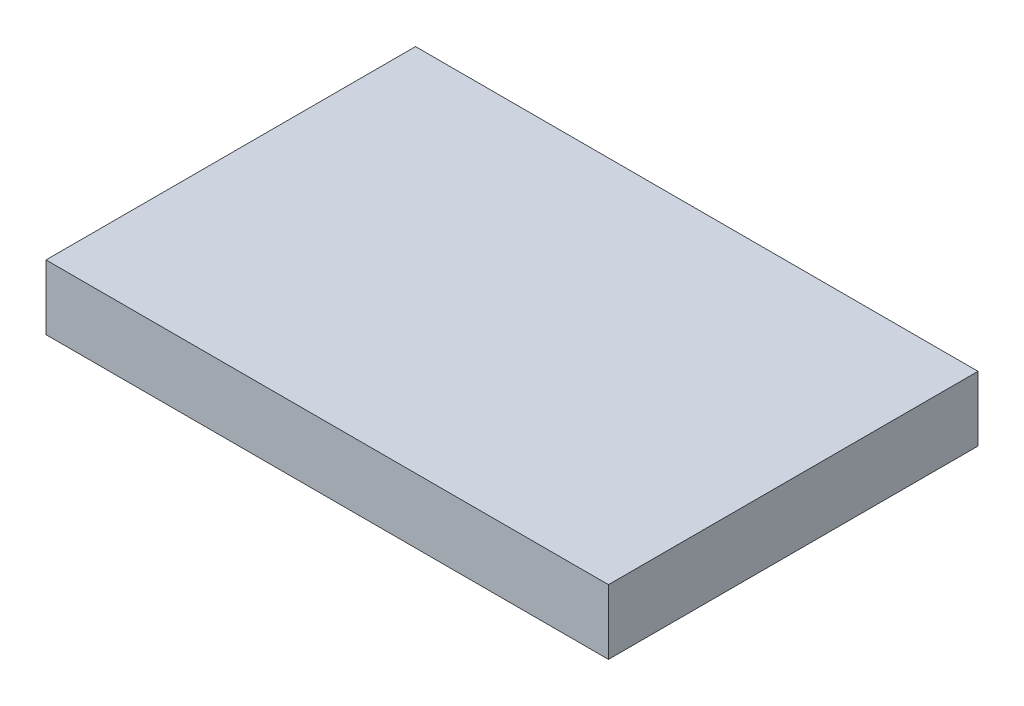
SolidWorks part; units mm, degrees
ref_plane "Front Plane" through (0, 0, 0) normal (0, 0, 1) x (1, 0, 0)
ref_plane "Top Plane" through (0, 0, 0) normal (0, 1, 0) x (1, 0, 0)
ref_plane "Right Plane" through (0, 0, 0) normal (1, 0, 0) x (0, 0, -1)
sketch "Sketch1" plane through (0, 0, 0) normal (0, 1, 0) x (1, 0, 0)
  line L1 (0, 0) -> (86, 0)
  line L2 (0, 0) -> (0, 56.5)
  line L3 (0, 56.5) -> (86, 56.5)
  line L4 (86, 0) -> (86, 56.5)
  dimension "D1" = 56.5
  dimension "D2" = 86
extrude "Boss-Extrude1" add sketch "Sketch1" along normal blind 9.9
